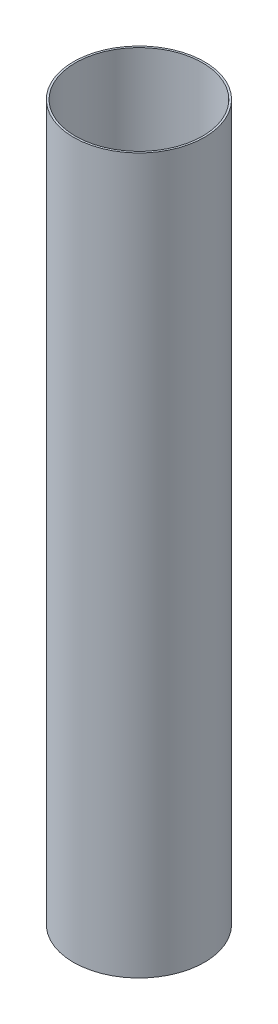
SolidWorks part; units mm, degrees
material "PVC Rígido"
ref_plane "Alzado" through (0, 0, 0) normal (0, 0, 1) x (1, 0, 0)
ref_plane "Planta" through (0, 0, 0) normal (0, 1, 0) x (1, 0, 0)
ref_plane "Vista lateral" through (0, 0, 0) normal (1, 0, 0) x (0, 0, -1)
sketch "Croquis1" plane through (0, 0, 0) normal (0, 1, 0) x (1, 0, 0)
  circle A0 centre (0, 0) radius 55
  circle A1 centre (0, 0) radius 53.4
  dimension "D1" = 110
  dimension "D2" = 1.6
extrude "Saliente-Extruir1" add sketch "Croquis1" along normal blind 600
